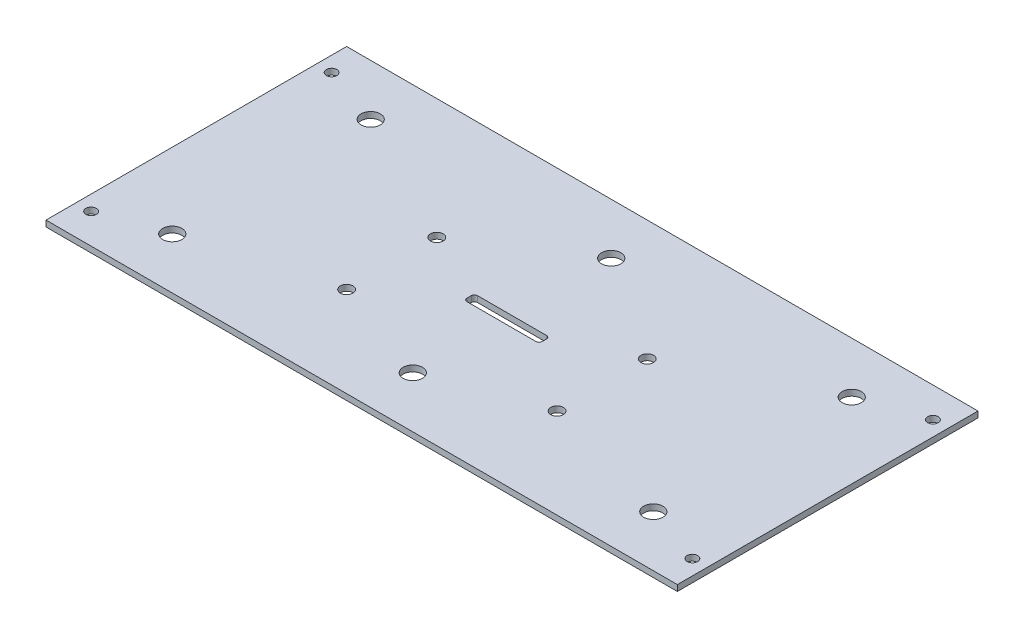
SolidWorks part; units mm, degrees
material "1060 Сплав"
ref_plane "Спереди" through (0, 0, 0) normal (0, 0, 1) x (1, 0, 0)
ref_plane "Сверху" through (0, 0, 0) normal (0, 1, 0) x (1, 0, 0)
ref_plane "Справа" through (0, 0, 0) normal (1, 0, 0) x (0, 0, -1)
sketch "Эскиз1" plane through (0, 0, 0) normal (0, 1, 0) x (1, 0, 0)
  line L5 (0, 0) -> (210, 0)
  line L6 (0, 0) -> (0, 100)
  line L7 (0, 100) -> (210, 100)
  line L8 (210, 0) -> (210, 100)
  line L9 (0, 50) -> (210, 50) construction
  line L10 (105, 100) -> (105, 0) construction
  circle A0 centre (105, 17) radius 3.2
  circle A1 centre (185, 17) radius 3.2
  circle A2 centre (25, 17) radius 3.2
  circle A3 centre (25, 83) radius 3.2
  circle A4 centre (105, 83) radius 3.2
  circle A5 centre (185, 83) radius 3.2
  circle A6 centre (5, 10) radius 1.75
  circle A7 centre (5, 90) radius 1.75
  circle A8 centre (205, 10) radius 1.75
  circle A9 centre (205, 90) radius 1.75
  dimension "D3" = 17
  dimension "D5" = 6.4
  dimension "D6" = 6.4
  dimension "D7" = 3.5
  dimension "D1" = 210
  dimension "D2" = 100
  dimension "D4" = 80
  dimension "D8" = 10
  dimension "D9" = 5
extrude "Бобышка-Вытянуть1" add sketch "Эскиз1" along normal blind 2
hole_wizard "Сверло под метчик  спиральное M41" positions "Эскиз2" profile "Эскиз3" hole size "M4x0.7" standard "DIN"
sketch "Эскиз2" plane through (0, 2, 0) normal (0, 1, 0) x (1, 0, 0)
  line L1 (0, 100) -> (0, 0) construction
  line L3 (210, 100) -> (0, 100) construction
  point P0 (70, 60)
  point P3 (140, 60)
  point P6 (140, 30)
  point P8 (70, 30)
  point P22 (0, 0)
  point P23 (0, 0)
  dimension "D1" = 70
  dimension "D2" = 30
  dimension "D3" = 70
  dimension "D4" = 40
sketch "Эскиз3" plane through (70, 2, -60) normal (1, 0, 0) x (0, 0, 1)
  line L0 (0, 0) -> (0, 9.2618)
  line L1 (0, 9.2618) -> (2.1, 8)
  line L2 (2.1, 8) -> (2.1, 0)
  line L5 (2.1, 0) -> (0, 0)
  line L10 (0, 9.2618) -> (-2.1, 8) construction
  line L11 (0, -6.35) -> (0, 107.95) construction
  dimension "Диаметр отверстия" = 4.2
  dimension "Глубина отверстия" = 8
  dimension "Угол заточки сверла" = 118
sketch "Эскиз4" plane through (0, 2, 0) normal (0, 1, 0) x (1, 0, 0)
  line L0 (210, 100) -> (0, 100) construction
  line L1 (92.5, 50) -> (117.5, 50)
  line L2 (92.5, 50) -> (92.5, 46.5)
  line L3 (92.5, 46.5) -> (117.5, 46.5)
  line L4 (117.5, 50) -> (117.5, 46.5)
  point P4 (105, 50)
  point P5 (105, 100)
  point P6 (0, 0)
  dimension "D1" = 50
  dimension "D2" = 3.5
  dimension "D3" = 25
extrude "Вырез-Вытянуть1" cut sketch "Эскиз4" against normal blind 10
fillet "Скругление1" radius 1 4 edges at (117.5, 1, -46.5) (117.5, 1, -50) (92.5, 1, -50) (92.5, 1, -46.5)
